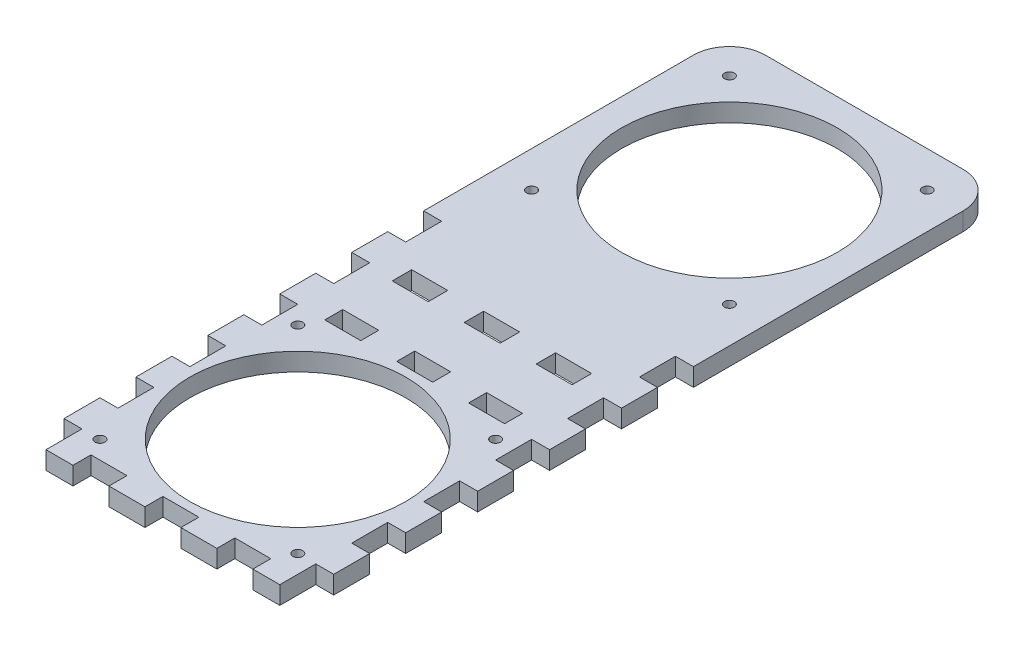
SolidWorks part; units mm, degrees
material "Pine"
ref_plane "Front Plane" through (0, 0, 0) normal (0, 0, 1) x (1, 0, 0)
ref_plane "Top Plane" through (0, 0, 0) normal (0, 1, 0) x (1, 0, 0)
ref_plane "Right Plane" through (0, 0, 0) normal (1, 0, 0) x (0, 0, -1)
sketch "Sketch1" plane through (0, 0, 0) normal (0, 1, 0) x (1, 0, 0)
  line L1 (0, 0) -> (95.25, 0)
  line L2 (0, 0) -> (0, 247.65)
  line L3 (0, 247.65) -> (95.25, 247.65)
  line L4 (95.25, 0) -> (95.25, 247.65)
  dimension "D1" = 95.25
  dimension "D2" = 247.65
extrude "Boss-Extrude1" add sketch "Sketch1" along normal blind 6.35
sketch "Sketch2" plane through (0, 6.35, 0) normal (0, 1, 0) x (1, 0, 0)
  line L0 (47.625, 247.65) -> (47.625, 0) construction
  line L1 (95.25, 247.65) -> (0, 247.65) construction
  line L2 (0, 0) -> (95.25, 0) construction
  circle A0 centre (47.625, 200.025) radius 38.1
  circle A1 centre (47.625, 47.625) radius 38.1
  dimension "D1" = 76.2
  dimension "D2" = 47.625
  dimension "D3" = 47.625
extrude "Cut-Extrude1" cut sketch "Sketch2" against normal through all
sketch "Sketch3" plane through (0, 6.35, 0) normal (0, 1, 0) x (1, 0, 0)
  line L0 (0, 247.65) -> (0, 0) construction
  line L1 (0, 12.7) -> (6.35, 12.7)
  line L2 (0, 12.7) -> (0, 0)
  line L3 (0, 0) -> (6.35, 0)
  line L4 (6.35, 12.7) -> (6.35, 0)
  line L5 (95.25, 0) -> (95.25, 247.65) construction
  line L6 (95.25, 12.7) -> (88.9, 12.7)
  line L7 (95.25, 12.7) -> (95.25, 0)
  line L8 (95.25, 0) -> (88.9, 0)
  line L9 (88.9, 12.7) -> (88.9, 0)
  dimension "D2" = 12.7
  dimension "D3" = 6.35
extrude "Cut-Extrude2" cut sketch "Sketch3" against normal through all
pattern_linear "LPattern1" count 6 spacing 25.4 along (0, 0, -1) of "Cut-Extrude2"
sketch "Sketch4" plane through (0, 6.35, 0) normal (0, 1, 0) x (1, 0, 0)
  line L1 (6.35, 0) -> (88.9, 0) construction
  line L2 (41.275, 0) -> (53.975, 0)
  line L3 (41.275, 0) -> (41.275, 6.35)
  line L4 (41.275, 6.35) -> (53.975, 6.35)
  line L5 (53.975, 0) -> (53.975, 6.35)
  line L7 (15.875, 0) -> (28.575, 0)
  line L8 (15.875, 0) -> (15.875, 6.35)
  line L9 (15.875, 6.35) -> (28.575, 6.35)
  line L10 (28.575, 0) -> (28.575, 6.35)
  line L11 (66.675, 0) -> (79.375, 0)
  line L12 (66.675, 0) -> (66.675, 6.35)
  line L14 (66.675, 6.35) -> (79.375, 6.35)
  line L15 (79.375, 0) -> (79.375, 6.35)
  point P16 (47.625, 0)
  dimension "D1" = 12.7
  dimension "D2" = 6.35
  dimension "D3" = 12.7
  dimension "D4" = 12.7
extrude "Cut-Extrude3" cut sketch "Sketch4" against normal through all
sketch "Sketch5" plane through (0, 6.35, 0) normal (0, 1, 0) x (1, 0, 0)
  line L0 (6.35, 0) -> (15.875, 0) construction
  line L1 (15.875, 95.25) -> (28.575, 95.25)
  line L2 (15.875, 95.25) -> (15.875, 88.9)
  line L3 (15.875, 88.9) -> (28.575, 88.9)
  line L4 (28.575, 95.25) -> (28.575, 88.9)
  line L5 (41.275, 95.25) -> (53.975, 95.25)
  line L6 (41.275, 95.25) -> (41.275, 88.9)
  line L7 (41.275, 88.9) -> (53.975, 88.9)
  line L8 (53.975, 95.25) -> (53.975, 88.9)
  line L9 (66.675, 95.25) -> (79.375, 95.25)
  line L10 (66.675, 95.25) -> (66.675, 88.9)
  line L11 (66.675, 88.9) -> (79.375, 88.9)
  line L12 (79.375, 95.25) -> (79.375, 88.9)
  line L13 (79.375, 92.075) -> (95.25, 92.075) construction
  line L14 (95.25, 88.9) -> (95.25, 101.6) construction
  line L15 (15.875, 92.075) -> (0, 92.075) construction
  line L16 (0, 101.6) -> (0, 88.9) construction
  dimension "D1" = 88.9
  dimension "D2" = 6.35
  dimension "D3" = 12.7
  dimension "D4" = 12.7
  dimension "D5" = 12.7
extrude "Cut-Extrude4" cut sketch "Sketch5" against normal through all
sketch "Sketch7" plane through (0, 0, 0) normal (-1, 0, 0) x (0, 0, 1)
  line L0 (-145.7227, -298.45) -> (-124.2415, -52.9191)
  line L1 (0, 6.35) -> (-215.9, 6.35)
  line L2 (-215.9, 6.35) -> (-215.9, 0)
  line L3 (-38.1, -298.45) -> (-38.1, 6.35) construction
  line L4 (0, 6.35) -> (0, -298.45)
  line L5 (0, -298.45) -> (-145.7227, -298.45)
  line L6 (-101.6, -12.7) -> (-103.7695, -37.4973) construction
  line L7 (-165.1, 6.35) -> (-165.1, -29.3294) construction
  line L8 (-215.9, 0) -> (-124.2415, -52.9191)
  line L9 (-124.2415, -52.9191) -> (-119.0561, 6.35) construction
  line L10 (-119.0561, 6.35) -> (-118.5027, 12.6758)
  line L11 (-119.0561, 6.35) -> (-112.7303, 5.7966)
  line L12 (-118.5027, 12.6758) -> (-112.1768, 12.1224)
  line L13 (-112.7303, 5.7966) -> (-112.1768, 12.1224)
  line L14 (-114.3, 0) -> (-114.3, 6.35) construction
  line L15 (-112.7303, 5.7966) -> (-112.7303, 6.35) construction
  line L16 (-127, 0) -> (-114.3, 0) construction
  circle A0 centre (-103.7695, -37.4973) radius 1.75
  point P12 (-101.6, -12.7)
  point P21 (-119.6117, 0)
  dimension "D8" = 3.5
  dimension "D1" = 304.8
  dimension "D2" = 85
  dimension "D3" = 38.1
  dimension "D4" = 127
  dimension "D5" = 50.8
  dimension "D6" = 6.35
  dimension "D7" = 30
  dimension "D9" = 101.6
  dimension "D10" = 19.05
  dimension "D11" = 24.892
  dimension "D12" = 19.05
  dimension "D13" = 5
sketch "Sketch8" plane through (0, 6.35, 0) normal (0, 1, 0) x (1, 0, 0)
  line L0 (15.875, 95.25) -> (15.875, 88.9) construction
  line L1 (15.875, 119.6117) -> (28.575, 119.6117)
  line L2 (15.875, 119.6117) -> (15.875, 112.7303)
  line L3 (15.875, 112.7303) -> (28.575, 112.7303)
  line L4 (28.575, 119.6117) -> (28.575, 112.7303)
  line L5 (41.275, 119.6117) -> (53.975, 119.6117)
  line L6 (41.275, 119.6117) -> (41.275, 112.7303)
  line L7 (41.275, 112.7303) -> (53.975, 112.7303)
  line L8 (53.975, 119.6117) -> (53.975, 112.7303)
  line L9 (66.675, 119.6117) -> (79.375, 119.6117)
  line L10 (66.675, 119.6117) -> (66.675, 112.7303)
  line L11 (66.675, 112.7303) -> (79.375, 112.7303)
  line L12 (79.375, 119.6117) -> (79.375, 112.7303)
  line L13 (28.575, 88.9) -> (28.575, 95.25) construction
  line L14 (41.275, 95.25) -> (41.275, 88.9) construction
  line L15 (53.975, 88.9) -> (53.975, 95.25) construction
  line L16 (66.675, 95.25) -> (66.675, 88.9) construction
  line L17 (79.375, 88.9) -> (79.375, 95.25) construction
extrude "Cut-Extrude5" cut sketch "Sketch8" against normal through all
sketch "Sketch9" plane through (0, 6.35, 0) normal (0, 1, 0) x (1, 0, 0)
  line L1 (12.7, 12.7) -> (82.55, 12.7) construction
  line L2 (12.7, 12.7) -> (12.7, 82.55) construction
  line L3 (12.7, 82.55) -> (82.55, 82.55) construction
  line L4 (82.55, 12.7) -> (82.55, 82.55) construction
  line L5 (12.7, 12.7) -> (82.55, 82.55) construction
  line L6 (12.7, 82.55) -> (82.55, 12.7) construction
  circle A0 centre (12.7, 82.55) radius 1.75
  point P0 (47.625, 47.625)
  dimension "D2" = 3.5
  dimension "D1" = 69.85
extrude "Cut-Extrude6" cut sketch "Sketch9" against normal through all
pattern_circular "CirPattern1" count 4 over 360 about axis through (47.625, 0, -47.625) along (0, 1, 0) of "Cut-Extrude6"
fillet "Fillet1" radius 12.7 2 edges at (0, 3.175, -247.65) (95.25, 3.175, -247.65)
sketch "Sketch10" plane through (0, 6.35, 0) normal (0, 1, 0) x (1, 0, 0)
  line L1 (82.55, 165.1) -> (12.7, 165.1) construction
  line L2 (82.55, 165.1) -> (82.55, 234.95) construction
  line L3 (82.55, 234.95) -> (12.7, 234.95) construction
  line L4 (12.7, 165.1) -> (12.7, 234.95) construction
  line L5 (82.55, 165.1) -> (12.7, 234.95) construction
  line L6 (82.55, 234.95) -> (12.7, 165.1) construction
  circle A0 centre (12.7, 234.95) radius 1.75
  point P0 (47.625, 200.025)
  dimension "D3" = 3.5
  dimension "D1" = 69.85
  dimension "D2" = 69.85
extrude "Cut-Extrude7" cut sketch "Sketch10" against normal through all
pattern_circular "CirPattern2" count 4 over 360 about axis through (47.625, 0, -200.025) along (0, 1, 0) of "Cut-Extrude7"
